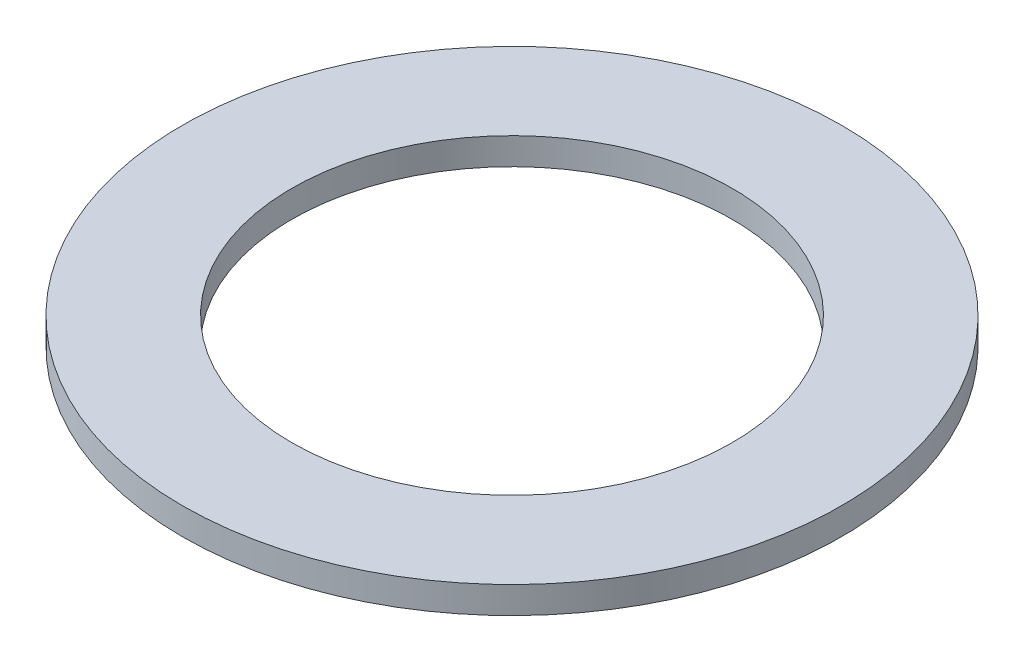
SolidWorks part; units mm, degrees
ref_plane "Front" through (0, 0, 0) normal (0, 0, 1) x (1, 0, 0)
ref_plane "Top" through (0, 0, 0) normal (0, 1, 0) x (1, 0, 0)
ref_plane "Right" through (0, 0, 0) normal (1, 0, 0) x (0, 0, -1)
sketch "Sketch1" plane through (0, 0, 0) normal (0, 1, 0) x (1, 0, 0)
  circle A0 centre (0, 0) radius 12.25
  circle A1 centre (0, 0) radius 8.1875
  dimension "D1" = 24.5
  dimension "D2" = 16.375
extrude "Boss-Extrude1" add sketch "Sketch1" along normal blind 1
